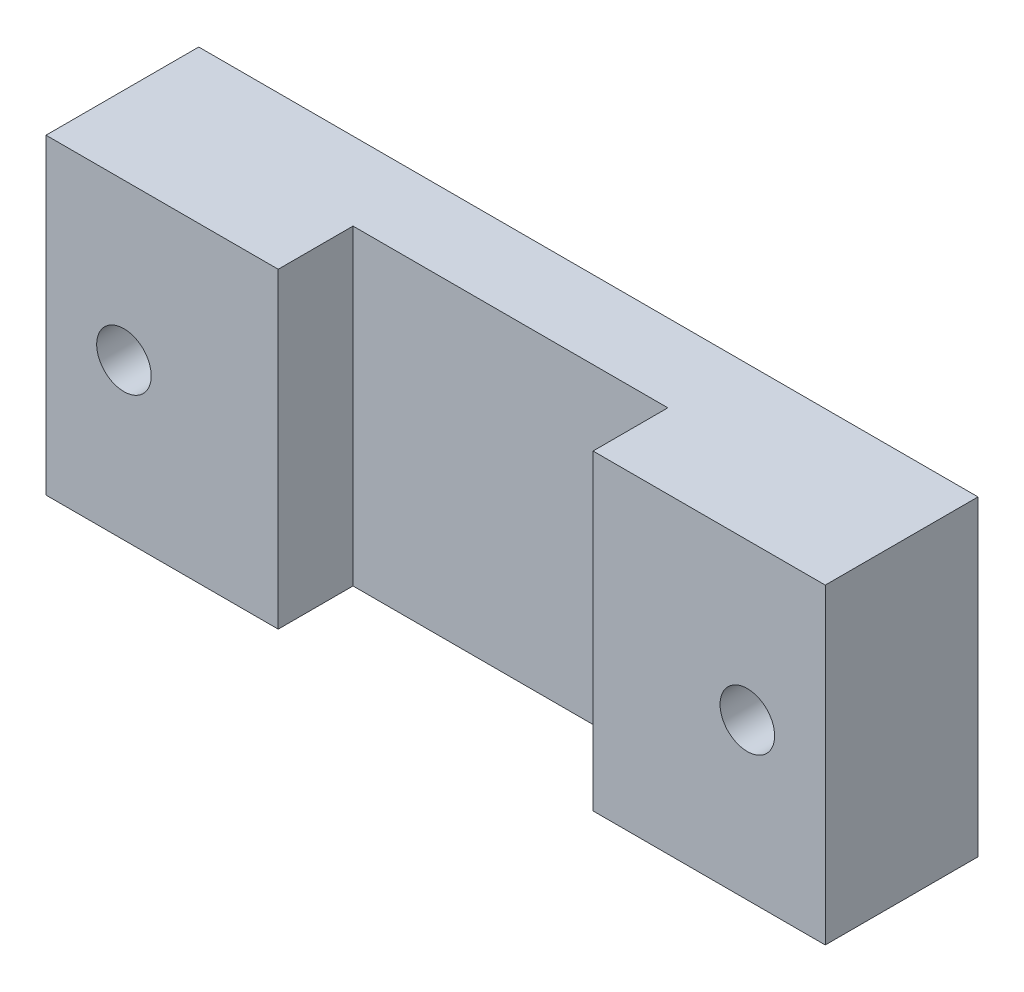
SolidWorks part; units mm, degrees
ref_plane "Спереди" through (0, 0, 0) normal (0, 0, 1) x (1, 0, 0)
ref_plane "Сверху" through (0, 0, 0) normal (0, 1, 0) x (1, 0, 0)
ref_plane "Справа" through (0, 0, 0) normal (1, 0, 0) x (0, 0, -1)
sketch "Sketch2" plane through (0, 0, 0) normal (0, 0, 1) x (1, 0, 0)
  line L0 (20, 0) -> (-20, 0) construction
  line L1 (25, -10) -> (-25, -10)
  line L2 (25, -10) -> (25, 10)
  line L3 (25, 10) -> (-25, 10)
  line L4 (-25, -10) -> (-25, 10)
  line L5 (25, -10) -> (-25, 10) construction
  line L6 (25, 10) -> (-25, -10) construction
  circle A0 centre (-20, 0) radius 1.75
  circle A1 centre (20, 0) radius 1.75
  point P0 (0, 0)
  point P9 (0, 0)
  dimension "D4" = 3.5
  dimension "D1" = 20
  dimension "D2" = 50
  dimension "D3" = 40
extrude "Boss-Extrude1" add sketch "Sketch2" along normal blind 5
sketch "Sketch5" plane through (0, -10, 0) normal (0, -1, 0) x (1, 0, 0)
  line L0 (-25, 5) -> (-25, 9.8)
  line L1 (-25, 5) -> (25, 5) construction
  line L2 (-25, 9.8) -> (-10.1, 9.8)
  line L3 (-10.1, 9.8) -> (-10.1, 5)
  line L4 (-10.1, 5) -> (10.1, 5)
  line L5 (10.1, 5) -> (10.1, 9.8)
  line L6 (10.1, 9.8) -> (25, 9.8)
  line L7 (25, 9.8) -> (25, 5)
  line L8 (25, 5) -> (-25, 5) construction
  line L9 (-25, 0) -> (25, 0) construction
  line L10 (0, 5) -> (0, 0) construction
  line L11 (25, 5) -> (25, 0) construction
  arc A0 (-25, 5) -> (25, 5) centre (0, 65) ccw
  point P15 (0, 0)
  point P18 (0, 0)
  dimension "D1" = 20.2
  dimension "D3" = 4.8
extrude "Boss-Extrude2" add sketch "Sketch5" against normal up to surface (20 mm away) up to face at (0, 10, 2.5)
sketch "Sketch6" plane through (0, 0, 0) normal (0, 0, -1) x (-1, 0, 0)
  circle A0 centre (20, 0) radius 1.75
  circle A1 centre (-20, 0) radius 1.75
  circle A2 centre (-20, 0) radius 1.75 construction
extrude "Cut-Extrude1" cut sketch "Sketch6" against normal through all
